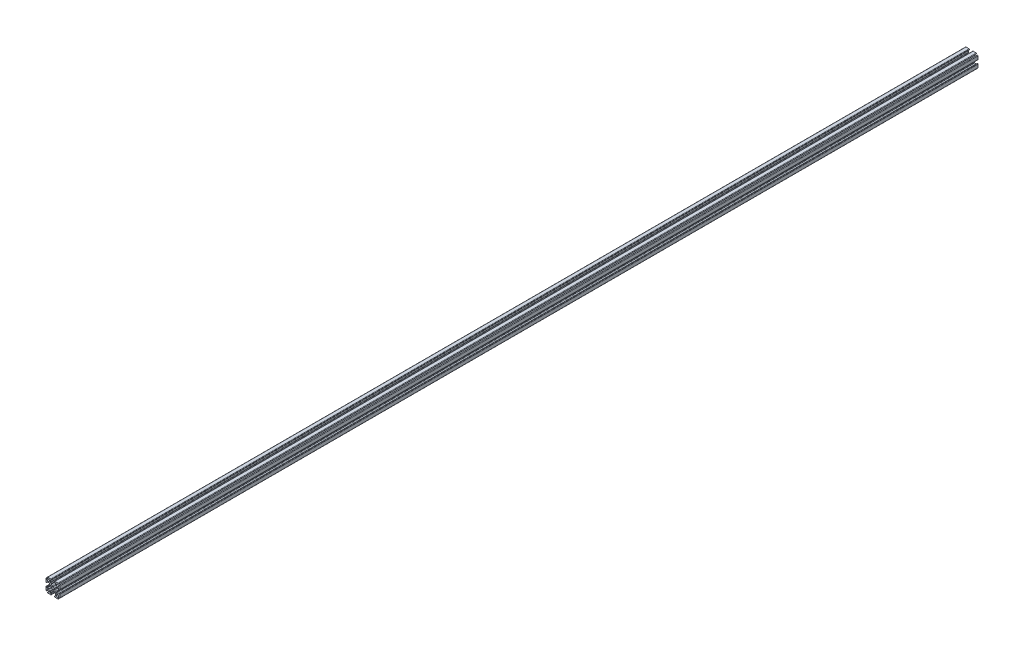
SolidWorks part; units mm, degrees
material "6061-T6 (SS)"
ref_plane "Front Plane" through (0, 0, 0) normal (0, 0, 1) x (1, 0, 0)
ref_plane "Top Plane" through (0, 0, 0) normal (0, 1, 0) x (1, 0, 0)
ref_plane "Right Plane" through (0, 0, 0) normal (1, 0, 0) x (0, 0, -1)
ref_plane "Plane1" through (0, 0, 0) normal (0, 0, -1) x (-1, 0, 0)
sketch "Sketch1" plane through (0, 0, 0) normal (0, 0, -1) x (-1, 0, 0)
  line L0 (6.6464, 5.9393) -> (6.1636, 5.4565)
  line L1 (5.4565, 6.1636) -> (5.9393, 6.6464)
  line L2 (5.5858, 7.5) -> (2.25, 7.5)
  line L3 (1.75, 7) -> (1.75, 6.8)
  line L4 (2.25, 6.3) -> (2.65, 6.3)
  line L5 (2.85, 6.1) -> (2.85, 4)
  line L6 (2.35, 3.5) -> (2.1, 3.5)
  line L7 (0.6, 2) -> (-0.6, 2)
  line L8 (-2.1, 3.5) -> (-2.35, 3.5)
  line L9 (-2.85, 4) -> (-2.85, 6.1)
  line L10 (-2.65, 6.3) -> (-2.25, 6.3)
  line L11 (-1.75, 6.8) -> (-1.75, 7)
  line L12 (-2.25, 7.5) -> (-5.5858, 7.5)
  line L13 (-5.9393, 6.6464) -> (-5.4565, 6.1636)
  line L14 (-6.1636, 5.4565) -> (-6.6464, 5.9393)
  line L15 (-7.5, 5.5858) -> (-7.5, 2.25)
  line L16 (-7, 1.75) -> (-6.8, 1.75)
  line L17 (-6.3, 2.25) -> (-6.3, 2.65)
  line L18 (-6.1, 2.85) -> (-4, 2.85)
  line L19 (-3.5, 2.35) -> (-3.5, 2.1)
  line L20 (-2, 0.6) -> (-2, -0.6)
  line L21 (-3.5, -2.1) -> (-3.5, -2.35)
  line L22 (-4, -2.85) -> (-6.1, -2.85)
  line L23 (-6.3, -2.65) -> (-6.3, -2.25)
  line L24 (-6.8, -1.75) -> (-7, -1.75)
  line L25 (-7.5, -2.25) -> (-7.5, -5.5858)
  line L26 (-6.6464, -5.9393) -> (-6.1636, -5.4565)
  line L27 (-5.4565, -6.1636) -> (-5.9393, -6.6464)
  line L28 (-5.5858, -7.5) -> (-2.25, -7.5)
  line L29 (-1.75, -7) -> (-1.75, -6.8)
  line L30 (-2.25, -6.3) -> (-2.65, -6.3)
  line L31 (-2.85, -6.1) -> (-2.85, -4)
  line L32 (-2.35, -3.5) -> (-2.1, -3.5)
  line L33 (-0.6, -2) -> (0.6, -2)
  line L34 (2.1, -3.5) -> (2.35, -3.5)
  line L35 (2.85, -4) -> (2.85, -6.1)
  line L36 (2.65, -6.3) -> (2.25, -6.3)
  line L37 (1.75, -6.8) -> (1.75, -7)
  line L38 (2.25, -7.5) -> (5.5858, -7.5)
  line L39 (5.9393, -6.6464) -> (5.4565, -6.1636)
  line L40 (6.1636, -5.4565) -> (6.6464, -5.9393)
  line L41 (7.5, -5.5858) -> (7.5, -2.25)
  line L42 (7, -1.75) -> (6.8, -1.75)
  line L43 (6.3, -2.25) -> (6.3, -2.65)
  line L44 (6.1, -2.85) -> (4, -2.85)
  line L45 (3.5, -2.35) -> (3.5, -2.1)
  line L46 (2, -0.6) -> (2, 0.6)
  line L47 (3.5, 2.1) -> (3.5, 2.35)
  line L48 (4, 2.85) -> (6.1, 2.85)
  line L49 (6.3, 2.65) -> (6.3, 2.25)
  line L50 (6.8, 1.75) -> (7, 1.75)
  line L51 (7.5, 2.25) -> (7.5, 5.5858)
  circle A0 centre (0, 0) radius 1.25
  arc A1 (6.1636, 5.4565) -> (5.4565, 6.1636) centre (5, 5) cw
  arc A2 (5.9393, 6.6464) -> (5.5858, 7.5) centre (5.5858, 7) ccw
  arc A3 (2.25, 7.5) -> (1.75, 7) centre (2.25, 7) ccw
  arc A4 (1.75, 6.8) -> (2.25, 6.3) centre (2.25, 6.8) ccw
  arc A5 (2.65, 6.3) -> (2.85, 6.1) centre (2.65, 6.1) cw
  arc A6 (2.85, 4) -> (2.35, 3.5) centre (2.35, 4) cw
  arc A7 (2.1, 3.5) -> (1.6, 3) centre (2.1, 3) ccw
  arc A8 (1.6, 3) -> (0.6, 2) centre (0.6, 3) cw
  arc A9 (-0.6, 2) -> (-1.6, 3) centre (-0.6, 3) cw
  arc A10 (-1.6, 3) -> (-2.1, 3.5) centre (-2.1, 3) ccw
  arc A11 (-2.35, 3.5) -> (-2.85, 4) centre (-2.35, 4) cw
  arc A12 (-2.85, 6.1) -> (-2.65, 6.3) centre (-2.65, 6.1) cw
  arc A13 (-2.25, 6.3) -> (-1.75, 6.8) centre (-2.25, 6.8) ccw
  arc A14 (-1.75, 7) -> (-2.25, 7.5) centre (-2.25, 7) ccw
  arc A15 (-5.5858, 7.5) -> (-5.9393, 6.6464) centre (-5.5858, 7) ccw
  arc A16 (-5.4565, 6.1636) -> (-6.1636, 5.4565) centre (-5, 5) cw
  arc A17 (-6.6464, 5.9393) -> (-7.5, 5.5858) centre (-7, 5.5858) ccw
  arc A18 (-7.5, 2.25) -> (-7, 1.75) centre (-7, 2.25) ccw
  arc A19 (-6.8, 1.75) -> (-6.3, 2.25) centre (-6.8, 2.25) ccw
  arc A20 (-6.3, 2.65) -> (-6.1, 2.85) centre (-6.1, 2.65) cw
  arc A21 (-4, 2.85) -> (-3.5, 2.35) centre (-4, 2.35) cw
  arc A22 (-3.5, 2.1) -> (-3, 1.6) centre (-3, 2.1) ccw
  arc A23 (-3, 1.6) -> (-2, 0.6) centre (-3, 0.6) cw
  arc A24 (-2, -0.6) -> (-3, -1.6) centre (-3, -0.6) cw
  arc A25 (-3, -1.6) -> (-3.5, -2.1) centre (-3, -2.1) ccw
  arc A26 (-3.5, -2.35) -> (-4, -2.85) centre (-4, -2.35) cw
  arc A27 (-6.1, -2.85) -> (-6.3, -2.65) centre (-6.1, -2.65) cw
  arc A28 (-6.3, -2.25) -> (-6.8, -1.75) centre (-6.8, -2.25) ccw
  arc A29 (-7, -1.75) -> (-7.5, -2.25) centre (-7, -2.25) ccw
  arc A30 (-7.5, -5.5858) -> (-6.6464, -5.9393) centre (-7, -5.5858) ccw
  arc A31 (-6.1636, -5.4565) -> (-5.4565, -6.1636) centre (-5, -5) cw
  arc A32 (-5.9393, -6.6464) -> (-5.5858, -7.5) centre (-5.5858, -7) ccw
  arc A33 (-2.25, -7.5) -> (-1.75, -7) centre (-2.25, -7) ccw
  arc A34 (-1.75, -6.8) -> (-2.25, -6.3) centre (-2.25, -6.8) ccw
  arc A35 (-2.65, -6.3) -> (-2.85, -6.1) centre (-2.65, -6.1) cw
  arc A36 (-2.85, -4) -> (-2.35, -3.5) centre (-2.35, -4) cw
  arc A37 (-2.1, -3.5) -> (-1.6, -3) centre (-2.1, -3) ccw
  arc A38 (-1.6, -3) -> (-0.6, -2) centre (-0.6, -3) cw
  arc A39 (0.6, -2) -> (1.6, -3) centre (0.6, -3) cw
  arc A40 (1.6, -3) -> (2.1, -3.5) centre (2.1, -3) ccw
  arc A41 (2.35, -3.5) -> (2.85, -4) centre (2.35, -4) cw
  arc A42 (2.85, -6.1) -> (2.65, -6.3) centre (2.65, -6.1) cw
  arc A43 (2.25, -6.3) -> (1.75, -6.8) centre (2.25, -6.8) ccw
  arc A44 (1.75, -7) -> (2.25, -7.5) centre (2.25, -7) ccw
  arc A45 (5.5858, -7.5) -> (5.9393, -6.6464) centre (5.5858, -7) ccw
  arc A46 (5.4565, -6.1636) -> (6.1636, -5.4565) centre (5, -5) cw
  arc A47 (6.6464, -5.9393) -> (7.5, -5.5858) centre (7, -5.5858) ccw
  arc A48 (7.5, -2.25) -> (7, -1.75) centre (7, -2.25) ccw
  arc A49 (6.8, -1.75) -> (6.3, -2.25) centre (6.8, -2.25) ccw
  arc A50 (6.3, -2.65) -> (6.1, -2.85) centre (6.1, -2.65) cw
  arc A51 (4, -2.85) -> (3.5, -2.35) centre (4, -2.35) cw
  arc A52 (3.5, -2.1) -> (3, -1.6) centre (3, -2.1) ccw
  arc A53 (3, -1.6) -> (2, -0.6) centre (3, -0.6) cw
  arc A54 (2, 0.6) -> (3, 1.6) centre (3, 0.6) cw
  arc A55 (3, 1.6) -> (3.5, 2.1) centre (3, 2.1) ccw
  arc A56 (3.5, 2.35) -> (4, 2.85) centre (4, 2.35) cw
  arc A57 (6.1, 2.85) -> (6.3, 2.65) centre (6.1, 2.65) cw
  arc A58 (6.3, 2.25) -> (6.8, 1.75) centre (6.8, 2.25) ccw
  arc A59 (7, 1.75) -> (7.5, 2.25) centre (7, 2.25) ccw
  arc A60 (7.5, 5.5858) -> (6.6464, 5.9393) centre (7, 5.5858) ccw
extrude "Length" add sketch "Sketch1" against normal blind 1000.0005
other "PropertyManager"
